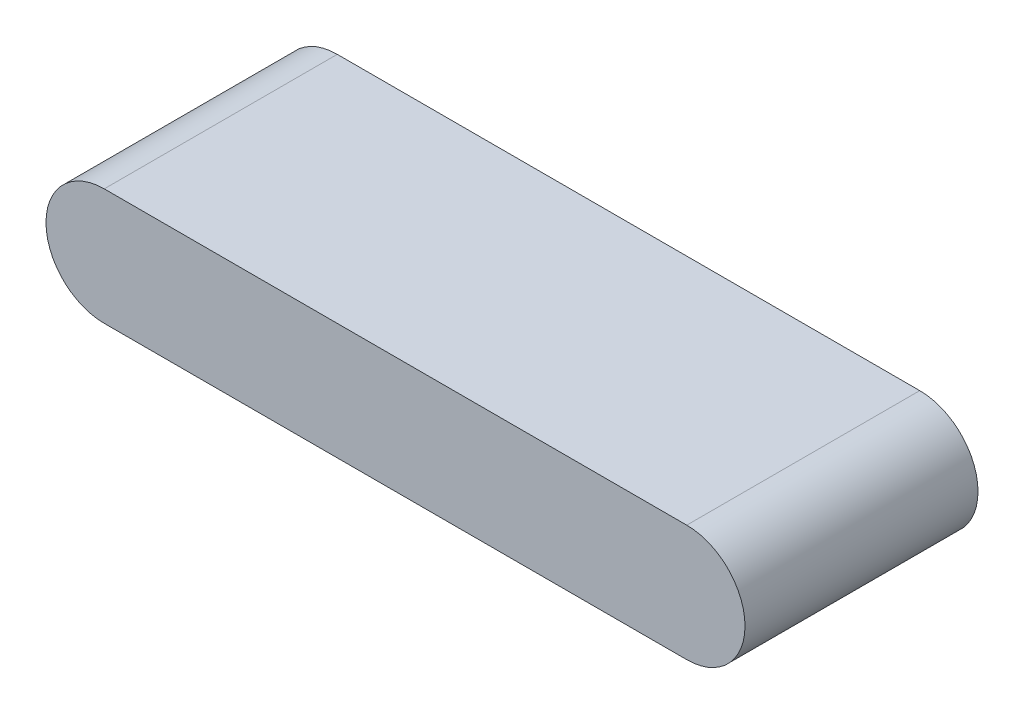
SolidWorks part; units mm, degrees
ref_plane "Front Plane" through (0, 0, 0) normal (0, 0, 1) x (1, 0, 0)
ref_plane "Top Plane" through (0, 0, 0) normal (0, 1, 0) x (1, 0, 0)
ref_plane "Right Plane" through (0, 0, 0) normal (1, 0, 0) x (0, 0, -1)
sketch "Sketch1" plane through (0, 0, 0) normal (0, 0, 1) x (1, 0, 0)
  line L0 (-53.7983, 0) -> (73.2017, 0) construction
  line L1 (-53.7983, 12.7) -> (73.2017, 12.7)
  line L2 (-53.7983, -12.7) -> (73.2017, -12.7)
  arc A0 (-53.7983, 12.7) -> (-53.7983, -12.7) centre (-53.7983, 0) ccw
  arc A1 (73.2017, -12.7) -> (73.2017, 12.7) centre (73.2017, 0) ccw
  point P3 (9.7017, 0)
extrude "Boss-Extrude1" add sketch "Sketch1" along normal mid plane 50.8
sketch "Sketch2" plane through (0, 12.7, 0) normal (0, 1, 0) x (1, 0, 0)
  line L0 (-53.7983, 0) -> (73.2017, 0) construction
  line L1 (-53.7983, -25.4) -> (-53.7983, 25.4) construction
  line L2 (73.2017, -25.4) -> (73.2017, 25.4) construction
